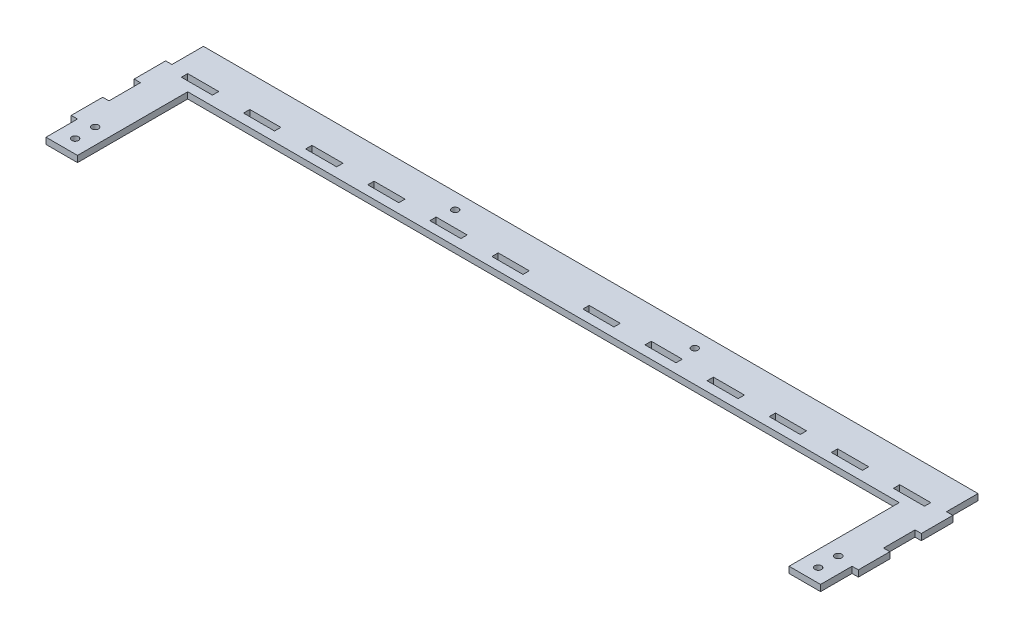
SolidWorks part; units mm, degrees
ref_plane "Front Plane" through (0, 0, 0) normal (0, 0, 1) x (1, 0, 0)
ref_plane "Top Plane" through (0, 0, 0) normal (0, 1, 0) x (1, 0, 0)
ref_plane "Right Plane" through (0, 0, 0) normal (1, 0, 0) x (0, 0, -1)
sketch "Sketch1" plane through (0, 0, 0) normal (0, 1, 0) x (1, 0, 0)
  line L0 (0, -24.6267) -> (0, 100.5806) construction
  line L1 (4, 0) -> (4, 20)
  line L2 (4, 20) -> (0, 20)
  line L3 (0, 20) -> (0, 40)
  line L4 (0, 40) -> (4, 40)
  line L5 (4, 40) -> (4, 60)
  line L6 (4, 60) -> (0, 60)
  line L7 (0, 60) -> (0, 80)
  line L8 (0, 80) -> (4, 80)
  line L9 (4, 80) -> (4, 100)
  line L10 (0, 0) -> (4, 0) construction
  line L11 (4, 0) -> (24, 0)
  line L12 (24, 0) -> (24, 70)
  line L13 (24, 70) -> (476, 70)
  line L16 (251.0496, 76) -> (-35.0505, 76) construction
  line L17 (14, 0) -> (14, 49.3314) construction
  line L18 (53.45, 76) -> (53.45, 80)
  line L19 (14, 76) -> (33.725, 76)
  line L20 (14, 76) -> (14, 80)
  line L21 (14, 80) -> (33.725, 80)
  line L22 (33.725, 76) -> (33.725, 80)
  line L23 (53.45, 76) -> (73.175, 76)
  line L24 (73.175, 76) -> (73.175, 80)
  line L25 (53.45, 80) -> (73.175, 80)
  line L26 (92.9, 76) -> (92.9, 80)
  line L27 (92.9, 76) -> (112.625, 76)
  line L28 (112.625, 76) -> (112.625, 80)
  line L29 (92.9, 80) -> (112.625, 80)
  line L30 (132.35, 76) -> (132.35, 80)
  line L31 (132.35, 76) -> (152.075, 76)
  line L32 (152.075, 76) -> (152.075, 80)
  line L33 (132.35, 80) -> (152.075, 80)
  line L34 (171.8, 76) -> (171.8, 80)
  line L35 (171.8, 76) -> (191.525, 76)
  line L36 (191.525, 76) -> (191.525, 80)
  line L37 (171.8, 80) -> (191.525, 80)
  line L38 (211.25, 76) -> (211.25, 80)
  line L39 (211.25, 76) -> (230.975, 76)
  line L40 (230.975, 76) -> (230.975, 80)
  line L41 (211.25, 80) -> (230.975, 80)
  line L42 (228.5555, 90) -> (146.8646, 90) construction
  line L43 (250, 70) -> (250, 140.3677) construction
  line L53 (4, 100) -> (250, 100)
  line L54 (271.4445, 90) -> (353.1354, 90) construction
  line L55 (486, 0) -> (486, 49.3314) construction
  line L56 (248.9504, 76) -> (535.0505, 76) construction
  line L57 (500, 0) -> (496, 0) construction
  line L58 (500, -24.6267) -> (500, 100.5806) construction
  line L59 (250, 100) -> (496, 100)
  line L60 (288.75, 80) -> (269.025, 80)
  line L61 (269.025, 76) -> (269.025, 80)
  line L62 (288.75, 76) -> (269.025, 76)
  line L63 (288.75, 76) -> (288.75, 80)
  line L64 (328.2, 80) -> (308.475, 80)
  line L65 (308.475, 76) -> (308.475, 80)
  line L66 (328.2, 76) -> (308.475, 76)
  line L67 (328.2, 76) -> (328.2, 80)
  line L68 (367.65, 80) -> (347.925, 80)
  line L69 (347.925, 76) -> (347.925, 80)
  line L70 (367.65, 76) -> (347.925, 76)
  line L71 (367.65, 76) -> (367.65, 80)
  line L72 (407.1, 80) -> (387.375, 80)
  line L73 (387.375, 76) -> (387.375, 80)
  line L74 (407.1, 76) -> (387.375, 76)
  line L75 (407.1, 76) -> (407.1, 80)
  line L76 (446.55, 80) -> (426.825, 80)
  line L77 (426.825, 76) -> (426.825, 80)
  line L78 (446.55, 76) -> (426.825, 76)
  line L79 (466.275, 76) -> (466.275, 80)
  line L80 (486, 80) -> (466.275, 80)
  line L81 (486, 76) -> (486, 80)
  line L82 (486, 76) -> (466.275, 76)
  line L83 (446.55, 76) -> (446.55, 80)
  line L84 (476, 0) -> (476, 70)
  line L85 (496, 0) -> (476, 0)
  line L86 (496, 80) -> (496, 100)
  line L87 (500, 80) -> (496, 80)
  line L88 (500, 60) -> (500, 80)
  line L89 (496, 60) -> (500, 60)
  line L90 (496, 40) -> (496, 60)
  line L91 (500, 40) -> (496, 40)
  line L92 (500, 20) -> (500, 40)
  line L93 (496, 20) -> (500, 20)
  line L94 (496, 0) -> (496, 20)
  circle A0 centre (14, 8.5) radius 2.125
  circle A1 centre (14, 21.25) radius 2.125
  circle A10 centre (173.885, 90) radius 2.125
  circle A11 centre (326.115, 90) radius 2.125
  circle A12 centre (486, 21.25) radius 2.125
  circle A13 centre (486, 8.5) radius 2.125
  point P61 (250, 100)
  dimension "D8" = 4.25
  dimension "D14" = 4.25
  dimension "D1" = 20
  dimension "D2" = 30
  dimension "D3" = 4
  dimension "D4" = 20
  dimension "D5" = 246
  dimension "D6" = 100
  dimension "D7" = 6
  dimension "D9" = 8.5
  dimension "D10" = 12.75
  dimension "D11" = 10
  dimension "D12" = 19.725
  dimension "D13" = 4
  dimension "D18" = 6
extrude "Boss-Extrude1" add sketch "Sketch1" along normal blind 4
